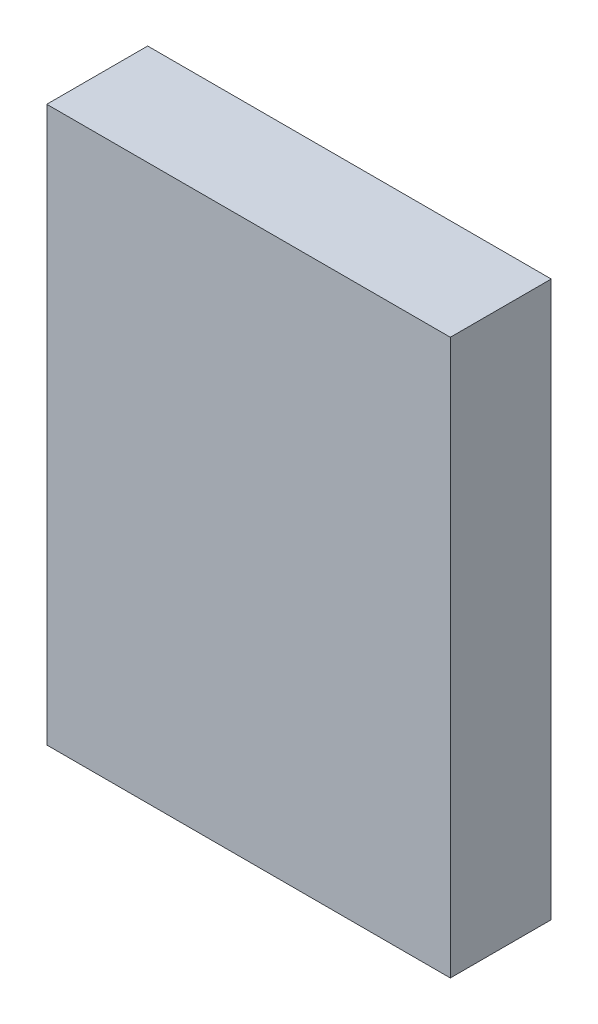
SolidWorks part; units mm, degrees
ref_plane "Front Plane" through (0, 0, 0) normal (0, 0, 1) x (1, 0, 0)
ref_plane "Top Plane" through (0, 0, 0) normal (0, 1, 0) x (1, 0, 0)
ref_plane "Right Plane" through (0, 0, 0) normal (1, 0, 0) x (0, 0, -1)
sketch "Sketch1" plane through (0, 0, 0) normal (0, 0, 1) x (1, 0, 0)
  line L0 (-10, 13.75) -> (10, -13.75) construction
  line L1 (-10, -13.75) -> (10, -13.75)
  line L2 (-10, -13.75) -> (-10, 13.75)
  line L3 (-10, 13.75) -> (10, 13.75)
  line L4 (10, -13.75) -> (10, 13.75)
  line L5 (10, 13.75) -> (0, 0) construction
  line L6 (0, 0) -> (-10, -13.75) construction
  dimension "D1" = 20
  dimension "D2" = 27.5
extrude "Boss-Extrude1" add sketch "Sketch1" along normal blind 5
